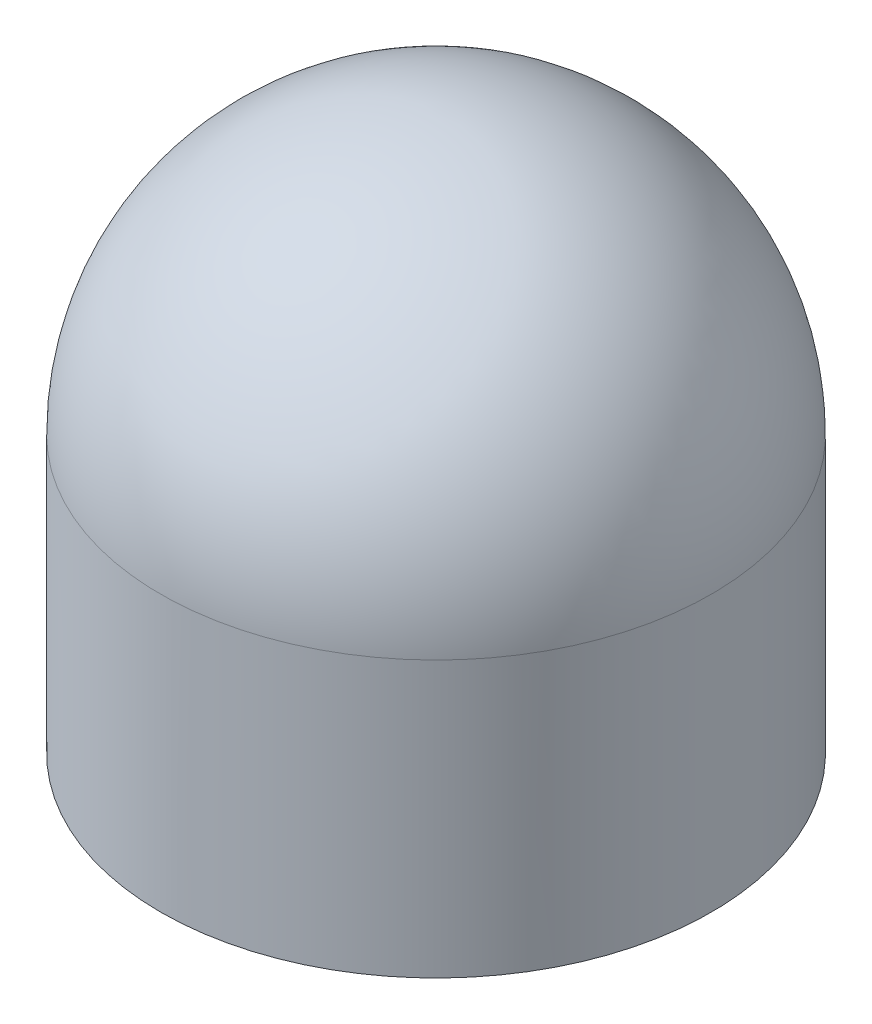
SolidWorks part; units mm, degrees
ref_plane "Plan de face" through (0, 0, 0) normal (0, 0, 1) x (1, 0, 0)
ref_plane "Plan de dessus" through (0, 0, 0) normal (0, 1, 0) x (1, 0, 0)
ref_plane "Plan de droite" through (0, 0, 0) normal (1, 0, 0) x (0, 0, -1)
sketch "Esquisse1" plane through (0, 0, 0) normal (0, 1, 0) x (1, 0, 0)
  circle A0 centre (0, 0) radius 2.5
  dimension "D1" = 5
extrude "Extrusion1" add sketch "Esquisse1" along normal blind 5
fillet "Congé1" radius 2.5 1 edges at (0, 5, 2.5)
